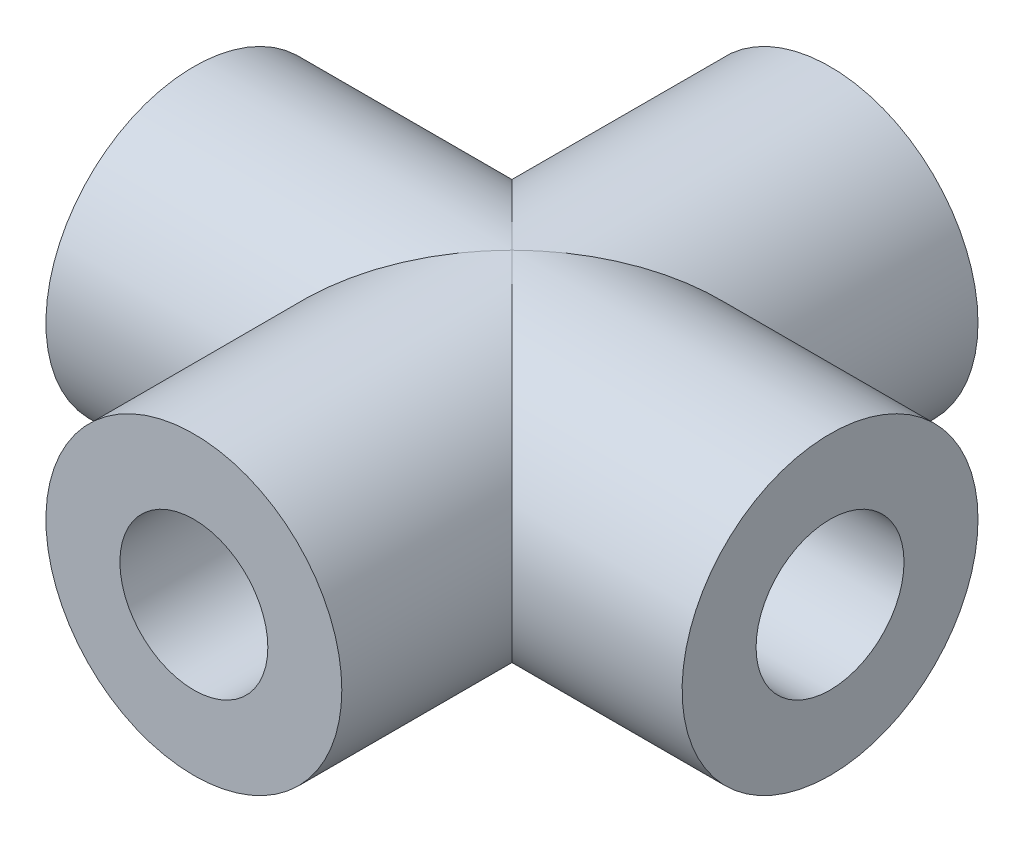
SolidWorks part; units mm, degrees
ref_plane "Front Plane" through (0, 0, 0) normal (0, 0, 1) x (1, 0, 0)
ref_plane "Top Plane" through (0, 0, 0) normal (0, 1, 0) x (1, 0, 0)
ref_plane "Right Plane" through (0, 0, 0) normal (1, 0, 0) x (0, 0, -1)
sketch "Sketch1" plane through (0, 0, 0) normal (0, 0, 1) x (1, 0, 0)
  circle A0 centre (0, 0) radius 12.7
  circle A1 centre (0, 0) radius 6.35
  dimension "D1" = 25.4
  dimension "D2" = 12.7
extrude "Boss-Extrude3" add sketch "Sketch1" along normal mid plane 54.61
sketch "Sketch2" plane through (0, 0, 0) normal (1, 0, 0) x (0, 0, -1)
  circle A0 centre (0, 0) radius 6.35
  circle A1 centre (0, 0) radius 12.7
  dimension "D1" = 25.4
  dimension "D2" = 12.7
extrude "Boss-Extrude4" add sketch "Sketch2" along normal mid plane 54.61 contours A1 | A0
